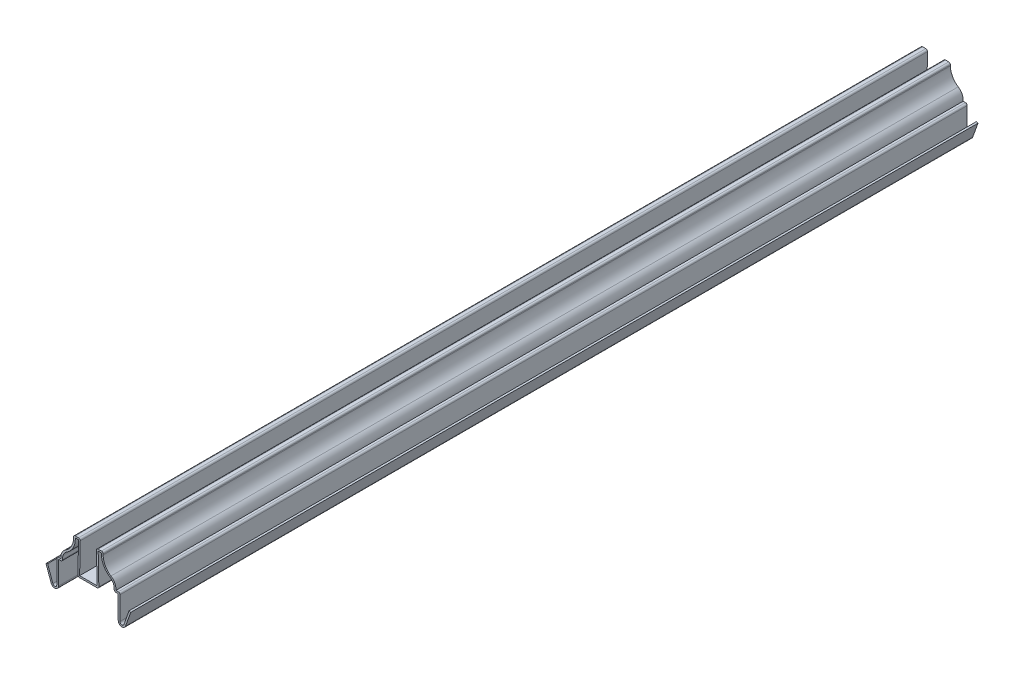
SolidWorks part; units mm, degrees
ref_plane "Front Plane" through (0, 0, 0) normal (0, 0, 1) x (1, 0, 0)
ref_plane "Top Plane" through (0, 0, 0) normal (0, 1, 0) x (1, 0, 0)
ref_plane "Right Plane" through (0, 0, 0) normal (1, 0, 0) x (0, 0, -1)
sketch "Sketch1" plane through (0, 0, 0) normal (0, 0, 1) x (1, 0, 0)
  line L0 (0, 0) -> (0, 19.0091) construction
  line L1 (-20.9438, 0) -> (20.9438, 0) construction
  line L2 (-24.0468, -1.732) -> (-20.9644, -10.3239)
  line L3 (-18.6531, -9.9219) -> (-18.6531, 4.7625)
  line L4 (-18.6531, 4.7625) -> (-16.2474, 4.7625)
  line L5 (-8.7312, 19.05) -> (-8.7312, 20.6375)
  line L6 (-8.7312, 20.6375) -> (-4.7625, 20.6375)
  line L7 (-4.7625, 20.6375) -> (-5.1594, 1.5875)
  line L8 (-5.1594, 1.5875) -> (5.1594, 1.5875)
  line L9 (-24.0468, -1.732) -> (-25.0031, -2.075) construction
  line L10 (24.0468, -1.732) -> (25.0031, -2.075) construction
  line L11 (4.7625, 20.6375) -> (5.1594, 1.5875)
  line L12 (8.7312, 20.6375) -> (4.7625, 20.6375)
  line L13 (8.7312, 19.05) -> (8.7312, 20.6375)
  line L14 (18.6531, 4.7625) -> (16.2474, 4.7625)
  line L15 (18.6531, -9.9219) -> (18.6531, 4.7625)
  line L16 (24.0468, -1.732) -> (20.9644, -10.3239)
  arc A0 (-20.9644, -10.3239) -> (-18.6531, -9.9219) centre (-19.8438, -9.9219) ccw
  arc A1 (-16.2474, 4.7625) -> (-13.3292, 10.6775) centre (-9.9219, 5.319) cw
  arc A2 (-13.3292, 10.6775) -> (-8.7312, 19.05) centre (-18.6531, 19.05) ccw
  arc A3 (13.3292, 10.6775) -> (8.7312, 19.05) centre (18.6531, 19.05) cw
  arc A4 (16.2474, 4.7625) -> (13.3292, 10.6775) centre (9.9219, 5.319) ccw
  arc A5 (20.9644, -10.3239) -> (18.6531, -9.9219) centre (19.8438, -9.9219) cw
  point P6 (0, 0)
  point P16 (-6.8801, 4.4628)
  point P22 (-16.2656, 2.8473)
  point P23 (0, 0)
  point P24 (-12.1876, 9.6925)
  point P25 (0, 0)
  point P37 (0, 1.5875)
  dimension "D5" = 1.1906
  dimension "D10" = 9.9219
  dimension "D11" = 6.35
  dimension "D1" = 37.3062
  dimension "D2" = 20.6375
  dimension "D3" = 11.1125
  dimension "D4" = 1.016
  dimension "D6" = 9.1281
  dimension "D7" = 9.525
  dimension "D8" = 0.3969
  dimension "D9" = 3.9688
  dimension "D12" = 15.875
  dimension "D13" = 1.5875
  dimension "D14" = 2.3813
  dimension "D15" = 19.05
  dimension "D16" = 6.35
extrude "Extrude-Thin1" add sketch "Sketch1" against normal blind 500.0625 thin
fillet "Fillet1" radius 1.016 10 edges at (-18.6531, 4.7625, -250.0312) (-15.0188, 3.7465, -250.0312) (-6.1968, 0.5715, -250.0312) (6.1968, 0.5715, -250.0312) (15.0188, 3.7465, -250.0312) (18.6531, 4.7625, -250.0312) (8.7312, 20.6375, -250.0312) (4.7625, 20.6375, -250.0312) (-8.7312, 20.6375, -250.0312) (-4.7625, 20.6375, -250.0312)
